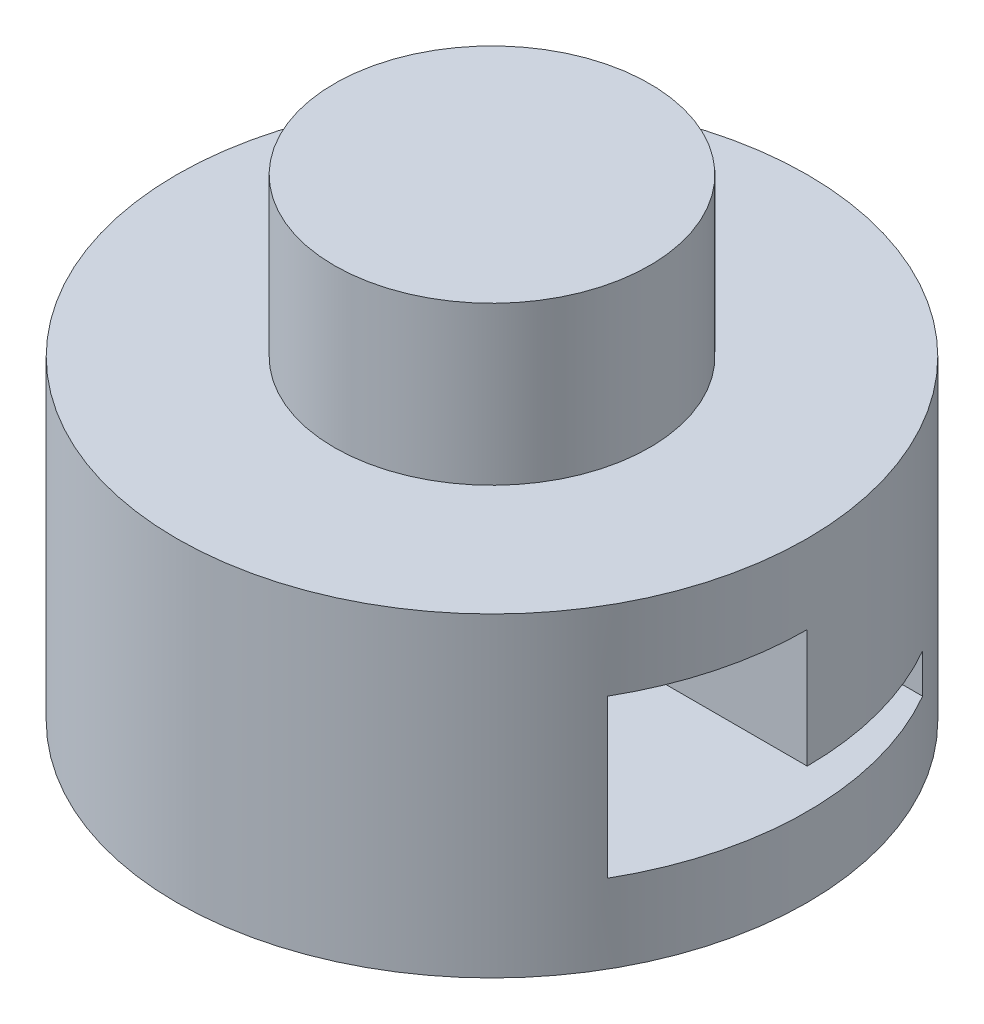
SolidWorks part; units mm, degrees
ref_plane "Front Plane" through (0, 0, 0) normal (0, 0, 1) x (1, 0, 0)
ref_plane "Top Plane" through (0, 0, 0) normal (0, 1, 0) x (1, 0, 0)
ref_plane "Right Plane" through (0, 0, 0) normal (1, 0, 0) x (0, 0, -1)
sketch "Sketch3" plane through (0, 0, 0) normal (0, 1, 0) x (1, 0, 0)
  circle A0 centre (0, 0) radius 25.4
  dimension "D1" = 50.8
extrude "Boss-Extrude1" add sketch "Sketch3" along normal blind 25.4
sketch "Sketch4" plane through (0, 25.4, 0) normal (0, 1, 0) x (1, 0, 0)
  circle A0 centre (0, 0) radius 12.7
  dimension "D1" = 25.4
extrude "Boss-Extrude2" add sketch "Sketch4" along normal blind 12.7
sketch "Sketch5" plane through (0, 0, 0) normal (1, 0, 0) x (0, 0, -1)
  line L0 (12.7, 6.35) -> (-12.7, 6.35)
  line L1 (-12.7, 6.35) -> (-12.7, 19.05)
  line L2 (-12.7, 19.05) -> (0, 19.05)
  line L3 (0, 19.05) -> (0, 9.525)
  line L4 (0, 9.525) -> (12.7, 9.525)
  line L5 (12.7, 9.525) -> (12.7, 6.35)
  line L6 (-25.4, 0) -> (25.4, 0) construction
  dimension "D1" = 12.7
  dimension "D2" = 12.7
  dimension "D3" = 3.175
  dimension "D4" = 25.4
  dimension "D5" = 12.7
  dimension "D6" = 6.35
extrude "Cut-Extrude1" cut sketch "Sketch5" against normal through all both and the other way through all
